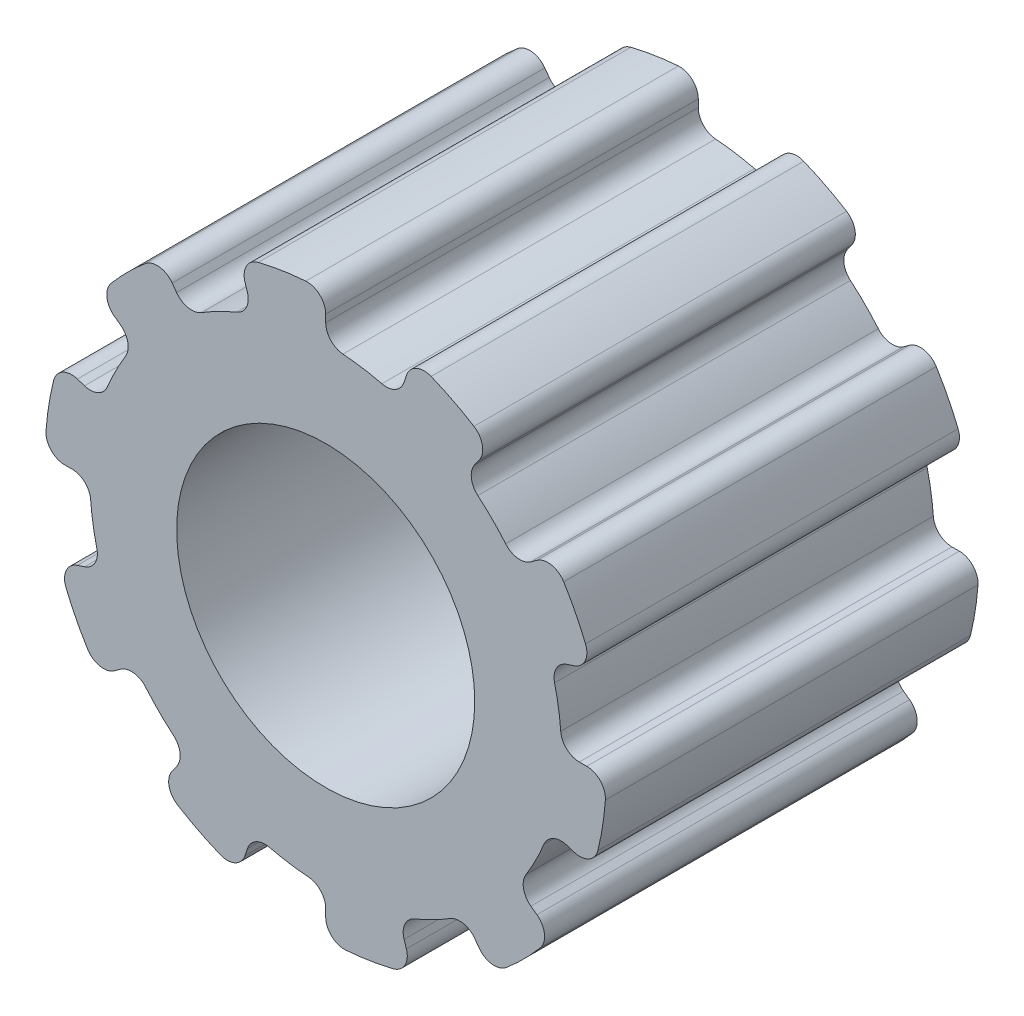
SolidWorks part; units mm, degrees
ref_plane "Plan de face" through (0, 0, 0) normal (0, 0, 1) x (1, 0, 0)
ref_plane "Plan de dessus" through (0, 0, 0) normal (0, 1, 0) x (1, 0, 0)
ref_plane "Plan de droite" through (0, 0, 0) normal (1, 0, 0) x (0, 0, -1)
sketch "Esquisse1" plane through (0, 0, 0) normal (0, 0, 1) x (1, 0, 0)
  line L0 (4.0009, 5.5067) -> (4.1187, 5.6689)
  line L1 (5.5067, 4.0009) -> (5.6689, 4.1187)
  line L2 (6.4735, 2.1034) -> (6.6642, 2.1653)
  line L3 (6.8067, 0) -> (7.0072, 0)
  line L4 (6.4735, -2.1034) -> (6.6642, -2.1653)
  line L5 (5.5067, -4.0009) -> (5.6689, -4.1187)
  line L6 (4.0009, -5.5067) -> (4.1187, -5.6689)
  line L7 (2.1034, -6.4735) -> (2.1653, -6.6642)
  line L8 (0, -6.8067) -> (0, -7.0072)
  line L9 (-2.1034, -6.4735) -> (-2.1653, -6.6642)
  line L10 (-4.0009, -5.5067) -> (-4.1187, -5.6689)
  line L11 (-5.5067, -4.0009) -> (-5.6689, -4.1187)
  line L12 (-6.4735, -2.1034) -> (-6.6642, -2.1653)
  line L13 (-6.8067, 0) -> (-7.0072, 0)
  line L14 (-6.4735, 2.1034) -> (-6.6642, 2.1653)
  line L15 (-5.5067, 4.0009) -> (-5.6689, 4.1187)
  line L16 (-4.0009, 5.5067) -> (-4.1187, 5.6689)
  line L17 (-2.1034, 6.4735) -> (-2.1653, 6.6642)
  line L20 (0, 6.8067) -> (0, 7.0072)
  line L21 (2.1034, 6.4735) -> (2.1653, 6.6642)
  arc A0 (-0.5356, 7.5059) -> (-1.8101, 7.3041) centre (0, 0) ccw
  circle A1 centre (0, 0) radius 4
  arc A2 (1.5086, 6.1425) -> (0.4634, 6.308) centre (0, 0) ccw
  arc A3 (3.9786, 6.3872) -> (2.8288, 6.973) centre (0, 0) ccw
  arc A4 (4.8309, 4.0826) -> (4.0826, 4.8309) centre (0, 0) ccw
  arc A5 (3.9786, 6.3872) -> (4.1187, 5.6689) centre (3.7142, 5.9628) cw
  arc A6 (-0.5356, 7.5059) -> (0, 7.0072) centre (-0.5, 7.0072) cw
  arc A7 (0, 6.8067) -> (0.4634, 6.308) centre (0.5, 6.8067) ccw
  arc A8 (2.1034, 6.4735) -> (1.5086, 6.1425) centre (1.6278, 6.628) cw
  arc A9 (2.8288, 6.973) -> (2.1653, 6.6642) centre (2.6409, 6.5097) ccw
  arc A10 (4.0009, 5.5067) -> (4.0826, 4.8309) centre (4.4054, 5.2128) ccw
  arc A11 (5.5067, 4.0009) -> (4.8309, 4.0826) centre (5.2128, 4.4054) cw
  arc A12 (6.3872, 3.9786) -> (5.6689, 4.1187) centre (5.9628, 3.7142) ccw
  arc A13 (6.973, 2.8288) -> (6.3872, 3.9786) centre (0, 0) ccw
  arc A14 (6.308, 0.4634) -> (6.1425, 1.5086) centre (0, 0) ccw
  arc A15 (6.973, 2.8288) -> (6.6642, 2.1653) centre (6.5097, 2.6409) cw
  arc A16 (6.4735, 2.1034) -> (6.1425, 1.5086) centre (6.628, 1.6278) ccw
  arc A17 (6.8067, 0) -> (6.308, 0.4634) centre (6.8067, 0.5) cw
  arc A18 (7.5059, -0.5356) -> (7.0072, 0) centre (7.0072, -0.5) ccw
  arc A19 (7.3041, -1.8101) -> (7.5059, -0.5356) centre (0, 0) ccw
  arc A20 (5.3756, -3.3329) -> (5.8561, -2.39) centre (0, 0) ccw
  arc A21 (7.3041, -1.8101) -> (6.6642, -2.1653) centre (6.8187, -1.6898) cw
  arc A22 (6.4735, -2.1034) -> (5.8561, -2.39) centre (6.319, -2.5789) ccw
  arc A23 (5.5067, -4.0009) -> (5.3756, -3.3329) centre (5.8006, -3.5963) cw
  arc A24 (5.7576, -4.8452) -> (5.6689, -4.1187) centre (5.375, -4.5232) ccw
  arc A25 (4.8452, -5.7576) -> (5.7576, -4.8452) centre (0, 0) ccw
  arc A26 (2.39, -5.8561) -> (3.3329, -5.3756) centre (0, 0) ccw
  arc A27 (4.8452, -5.7576) -> (4.1187, -5.6689) centre (4.5232, -5.375) cw
  arc A28 (4.0009, -5.5067) -> (3.3329, -5.3756) centre (3.5963, -5.8006) ccw
  arc A29 (2.1034, -6.4735) -> (2.39, -5.8561) centre (2.5789, -6.319) cw
  arc A30 (1.8101, -7.3041) -> (2.1653, -6.6642) centre (1.6898, -6.8187) ccw
  arc A31 (0.5356, -7.5059) -> (1.8101, -7.3041) centre (0, 0) ccw
  arc A32 (-1.5086, -6.1425) -> (-0.4634, -6.308) centre (0, 0) ccw
  arc A33 (0.5356, -7.5059) -> (0, -7.0072) centre (0.5, -7.0072) cw
  arc A34 (0, -6.8067) -> (-0.4634, -6.308) centre (-0.5, -6.8067) ccw
  arc A35 (-2.1034, -6.4735) -> (-1.5086, -6.1425) centre (-1.6278, -6.628) cw
  arc A36 (-2.8288, -6.973) -> (-2.1653, -6.6642) centre (-2.6409, -6.5097) ccw
  arc A37 (-3.9786, -6.3872) -> (-2.8288, -6.973) centre (0, 0) ccw
  arc A38 (-4.8309, -4.0826) -> (-4.0826, -4.8309) centre (0, 0) ccw
  arc A39 (-3.9786, -6.3872) -> (-4.1187, -5.6689) centre (-3.7142, -5.9628) cw
  arc A40 (-4.0009, -5.5067) -> (-4.0826, -4.8309) centre (-4.4054, -5.2128) ccw
  arc A41 (-5.5067, -4.0009) -> (-4.8309, -4.0826) centre (-5.2128, -4.4054) cw
  arc A42 (-6.3872, -3.9786) -> (-5.6689, -4.1187) centre (-5.9628, -3.7142) ccw
  arc A43 (-6.973, -2.8288) -> (-6.3872, -3.9786) centre (0, 0) ccw
  arc A44 (-6.308, -0.4634) -> (-6.1425, -1.5086) centre (0, 0) ccw
  arc A45 (-6.973, -2.8288) -> (-6.6642, -2.1653) centre (-6.5097, -2.6409) cw
  arc A46 (-6.4735, -2.1034) -> (-6.1425, -1.5086) centre (-6.628, -1.6278) ccw
  arc A47 (-6.8067, 0) -> (-6.308, -0.4634) centre (-6.8067, -0.5) cw
  arc A48 (-7.5059, 0.5356) -> (-7.0072, 0) centre (-7.0072, 0.5) ccw
  arc A49 (-7.3041, 1.8101) -> (-7.5059, 0.5356) centre (0, 0) ccw
  arc A50 (-5.3756, 3.3329) -> (-5.8561, 2.39) centre (0, 0) ccw
  arc A51 (-7.3041, 1.8101) -> (-6.6642, 2.1653) centre (-6.8187, 1.6898) cw
  arc A52 (-6.4735, 2.1034) -> (-5.8561, 2.39) centre (-6.319, 2.5789) ccw
  arc A53 (-5.5067, 4.0009) -> (-5.3756, 3.3329) centre (-5.8006, 3.5963) cw
  arc A54 (-5.7576, 4.8452) -> (-5.6689, 4.1187) centre (-5.375, 4.5232) ccw
  arc A55 (-4.8452, 5.7576) -> (-5.7576, 4.8452) centre (0, 0) ccw
  arc A56 (-2.39, 5.8561) -> (-3.3329, 5.3756) centre (0, 0) ccw
  arc A57 (-4.8452, 5.7576) -> (-4.1187, 5.6689) centre (-4.5232, 5.375) cw
  arc A58 (-4.0009, 5.5067) -> (-3.3329, 5.3756) centre (-3.5963, 5.8006) ccw
  arc A59 (-2.1034, 6.4735) -> (-2.39, 5.8561) centre (-2.5789, 6.319) cw
  arc A60 (-1.8101, 7.3041) -> (-2.1653, 6.6642) centre (-1.6898, 6.8187) ccw
  point P17 (0, 7.525)
  point P20 (4.4231, 6.0879)
  point P41 (7.1567, 2.3254)
  point P56 (7.1567, -2.3254)
  point P71 (4.4231, -6.0879)
  point P86 (0, -7.525)
  point P101 (-4.4231, -6.0879)
  point P116 (-7.1567, -2.3254)
  point P131 (-7.1567, 2.3254)
  point P146 (-4.4231, 6.0879)
  dimension "D2" = 0.5
extrude "Extrusion1" add sketch "Esquisse1" along normal blind 10
